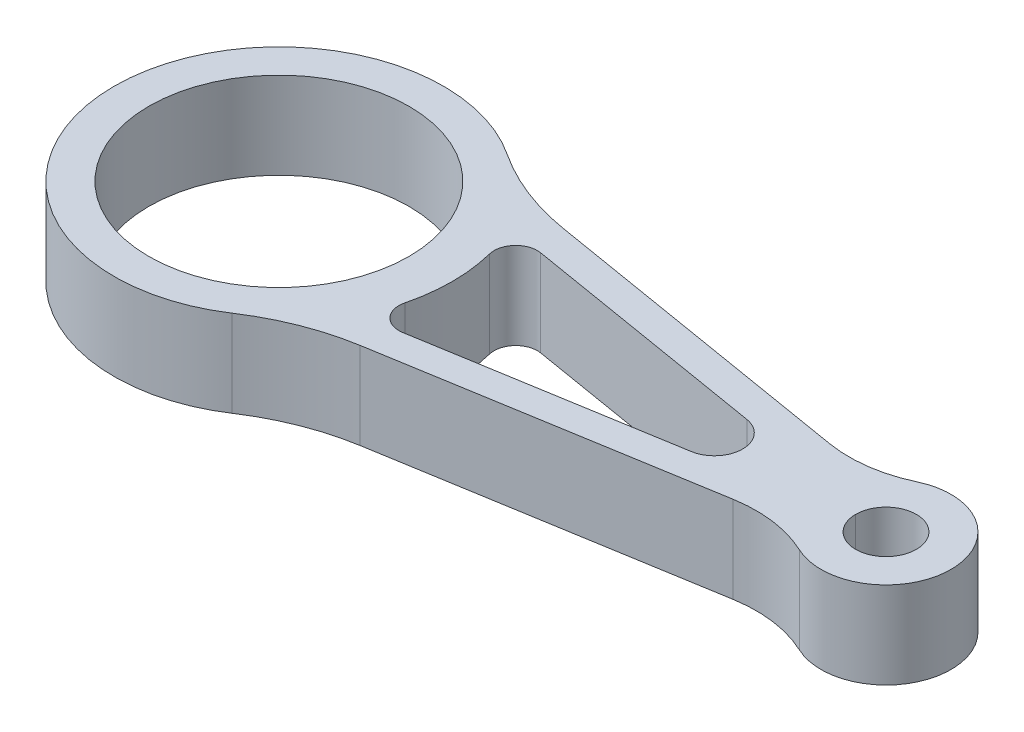
SolidWorks part; units mm, degrees
material "Plain Carbon Steel"
ref_plane "Front Plane" through (0, 0, 0) normal (0, 0, 1) x (1, 0, 0)
ref_plane "Top Plane" through (0, 0, 0) normal (0, 1, 0) x (1, 0, 0)
ref_plane "Right Plane" through (0, 0, 0) normal (1, 0, 0) x (0, 0, -1)
sketch "Sketch1" plane through (0, 0, 0) normal (0, 1, 0) x (1, 0, 0)
  line L0 (0, 0) -> (30, 0) construction
  line L1 (128.0638, 9.0844) -> (27.9355, 25.7606)
  line L2 (128.0638, -9.0844) -> (27.9355, -25.7606)
  line L3 (133, 0) -> (140, 0) construction
  circle A0 centre (0, 0) radius 30
  arc A1 (27.9355, 25.7606) -> (27.9355, -25.7606) centre (0, 0) ccw
  circle A2 centre (140, 0) radius 7
  arc A3 (128.0638, -9.0844) -> (128.0638, 9.0844) centre (140, 0) ccw
  dimension "D2" = 14
  dimension "D3" = 30
  dimension "D4" = 60
  dimension "D5" = 76
  dimension "D1" = 140
extrude "Boss-Extrude1" add sketch "Sketch1" along normal mid plane 20
sketch "Sketch2" plane through (0, 10, 0) normal (0, 1, 0) x (1, 0, 0)
  line L0 (0, 0) -> (176.1437, 0) construction
  line L1 (44.4614, 15.9118) -> (101.5026, 6.4117)
  line L2 (101.5026, -6.4117) -> (44.4614, -15.9118)
  line L3 (128.0638, 9.0844) -> (27.9355, 25.7606) construction
  arc A0 (38.7911, -9.7598) -> (38.7911, 9.7598) centre (0, 0) ccw
  arc A2 (101.5026, 6.4117) -> (101.5026, -6.4117) centre (100.4348, 0) cw
  arc A3 (44.4614, -15.9118) -> (38.7911, -9.7598) centre (43.6399, -10.9798) cw
  arc A4 (44.4614, 15.9118) -> (38.7911, 9.7598) centre (43.6399, 10.9798) ccw
  dimension "D1" = 80
  dimension "D2" = 6.5
  dimension "D4" = 5
  dimension "D3" = 7
extrude "Cut-Extrude1" cut sketch "Sketch2" against normal through all contours A0 A3 L2 A2 L1 A4
mirror "Mirror1" [suppressed] about plane through (0, 0, 0) normal (0, 1, 0)
fillet "Fillet1" radius 30 2 edges at (128.0638, 0, 9.0844) (128.0638, 0, -9.0844)
fillet "Fillet2" radius 55 2 edges at (27.9355, 0, 25.7606) (27.9355, 0, -25.7606)
split line "Split Line2"
